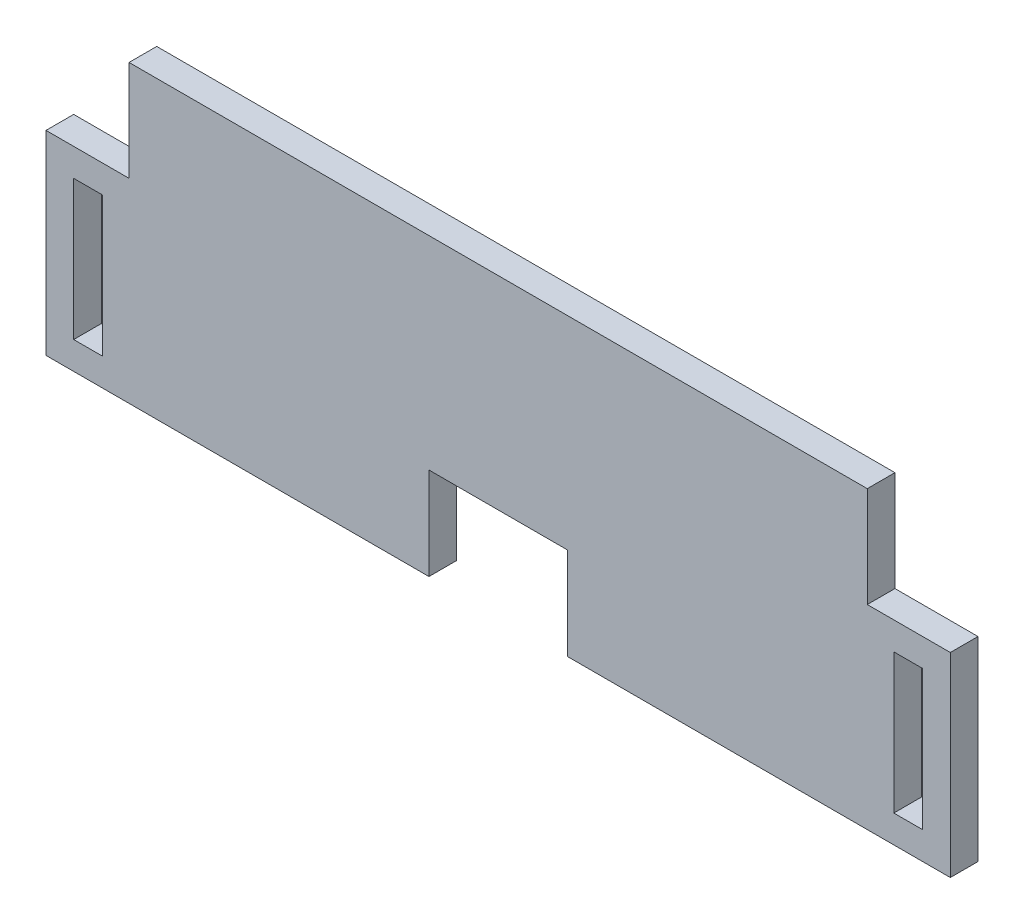
SolidWorks part; units mm, degrees
material "Pino"
ref_plane "Alzado" through (0, 0, 0) normal (0, 0, 1) x (1, 0, 0)
ref_plane "Planta" through (0, 0, 0) normal (0, 1, 0) x (1, 0, 0)
ref_plane "Vista lateral" through (0, 0, 0) normal (1, 0, 0) x (0, 0, -1)
sketch "Croquis1" plane through (0, 0, 0) normal (0, 0, 1) x (1, 0, 0)
  line L0 (-40, 21.123) -> (-49, 21.123)
  line L1 (40, 0) -> (-40, 0)
  line L2 (40, 0) -> (40, 32)
  line L3 (40, 32) -> (-40, 32)
  line L4 (-40, 0) -> (-40, 32)
  line L7 (-49, 21.123) -> (-49, 0)
  line L8 (-49, 0) -> (-40, 0)
  line L9 (0, 32) -> (0, 0) construction
  line L10 (42.877, 18.123) -> (42.877, 2.993)
  line L11 (-46, 18.123) -> (-42.877, 18.123)
  line L12 (-46, 18.123) -> (-46, 2.993)
  line L13 (-46, 2.993) -> (-42.877, 2.993)
  line L14 (-42.877, 18.123) -> (-42.877, 2.993)
  line L15 (46, 2.993) -> (42.877, 2.993)
  line L16 (46, 18.123) -> (46, 2.993)
  line L17 (46, 18.123) -> (42.877, 18.123)
  line L18 (49, 0) -> (40, 0)
  line L19 (49, 21.123) -> (49, 0)
  line L20 (40, 21.123) -> (49, 21.123)
  point P0 (0, 0)
extrude "Saliente-Extruir1" add sketch "Croquis1" along normal blind 3 contours L7 L8 L4 L0 L11 L14 L13 L12 | L9 L3 L4 L1 | L3 L9 L1 L2 | L20 L2 L18 L19 L17 L16 L15 L10
sketch "Croquis2" plane through (0, 0, 3) normal (0, 0, 1) x (1, 0, 0)
  line L0 (-7.5, 0) -> (7.5, 0)
  line L1 (-49, 0) -> (49, 0) construction
  line L2 (-7.5, 0) -> (-7.5, 10)
  line L3 (-7.5, 10) -> (7.5, 10)
  line L4 (7.5, 10) -> (7.5, 0)
  point P6 (0, 0)
  dimension "D1" = 15
  dimension "D2" = 10
extrude "Cortar-Extruir1" cut sketch "Croquis2" against normal through all contours L4 L0 L2 L3
equation "\"mdf_wid\"= 3mm"
equation "\"mdf_hei\"= 15mm"
equation "\"alturagato\"= 110mm"
equation "\"separacion\"= 13mm"
equation "\"D1@Croquis1\"=\"mdf_hei\"+6+0.123"
equation "\"up\"= 80mm"
equation "\"down\"= 170mm"
equation "\"D2@Croquis1\"=\"up\""
equation "\"D3@Croquis1\"=\"up\"/2.5"
equation "\"D4@Croquis1\"=\"mdf_wid\"*3"
equation "\"D5@Croquis1\"=\"mdf_wid\""
equation "\"D6@Croquis1\"=\"mdf_wid\""
equation "\"D8@Croquis1\"=\"mdf_wid\"+0.123"
